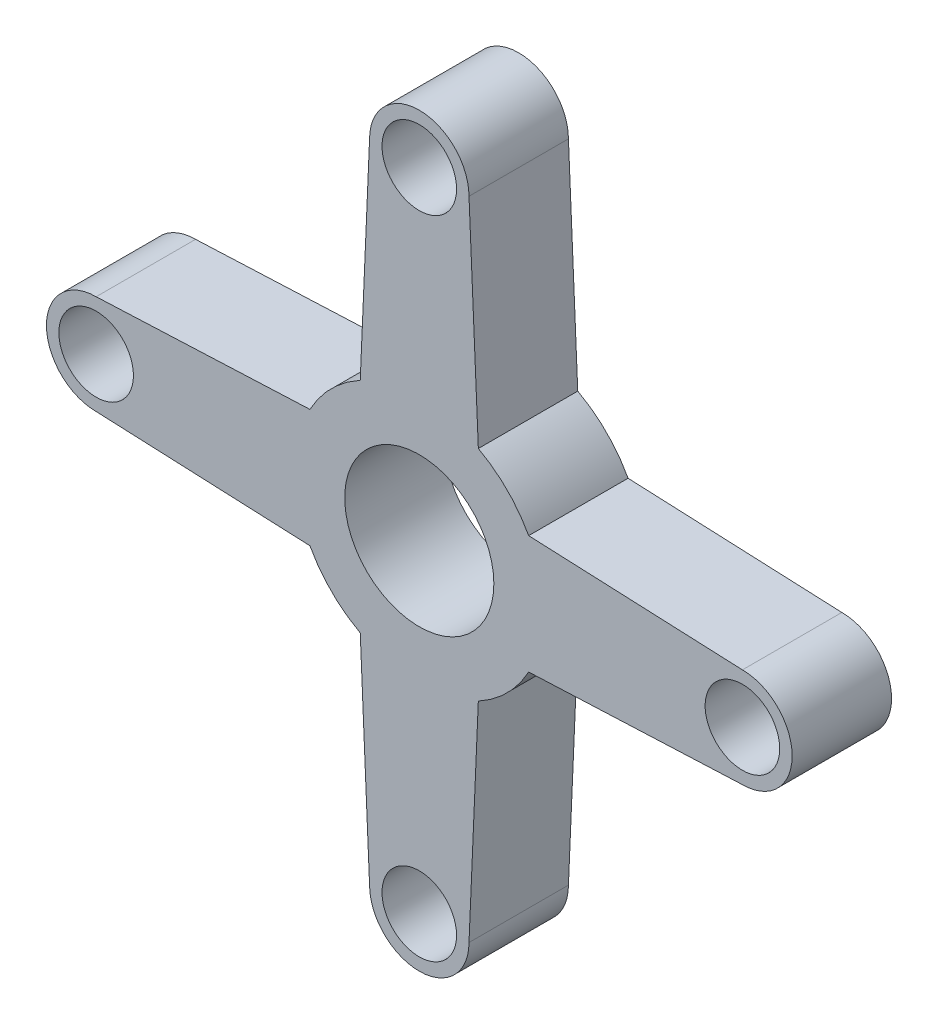
SolidWorks part; units mm, degrees
ref_plane "Front Plane" through (0, 0, 0) normal (0, 0, 1) x (1, 0, 0)
ref_plane "Top Plane" through (0, 0, 0) normal (0, 1, 0) x (1, 0, 0)
ref_plane "Right Plane" through (0, 0, 0) normal (1, 0, 0) x (0, 0, -1)
sketch "Sketch1" plane through (0, 0, 0) normal (0, 0, 1) x (1, 0, 0)
  line L0 (2, 13) -> (2.3755, 4.3997)
  line L1 (0, 0) -> (0, 13) construction
  line L2 (-2, 13) -> (-2.3755, 4.3997)
  line L3 (13, -2) -> (4.3997, -2.3755)
  line L4 (13, 2) -> (4.3997, 2.3755)
  line L5 (-2, -13) -> (-2.3755, -4.3997)
  line L6 (2, -13) -> (2.3755, -4.3997)
  line L7 (-13, 2) -> (-4.3997, 2.3755)
  line L8 (-13, -2) -> (-4.3997, -2.3755)
  circle A0 centre (0, 0) radius 3
  arc A1 (2, 13) -> (-2, 13) centre (0, 13) ccw
  arc A2 (13, -2) -> (13, 2) centre (13, 0) ccw
  arc A3 (-2, -13) -> (2, -13) centre (0, -13) ccw
  arc A4 (-13, 2) -> (-13, -2) centre (-13, 0) ccw
  arc A5 (4.3997, 2.3755) -> (2.3755, 4.3997) centre (0, 0) ccw
  arc A6 (-2.3755, 4.3997) -> (-4.3997, 2.3755) centre (0, 0) ccw
  arc A7 (-4.3997, -2.3755) -> (-2.3755, -4.3997) centre (0, 0) ccw
  arc A8 (2.3755, -4.3997) -> (4.3997, -2.3755) centre (0, 0) ccw
  circle A9 centre (0, 13) radius 1.5
  circle A10 centre (13, 0) radius 1.5
  circle A11 centre (0, -13) radius 1.5
  circle A12 centre (-13, 0) radius 1.5
  point P14 (0, 0)
  point P32 (0, 0)
  dimension "D1" = 6
  dimension "D2" = 4
  dimension "D5" = 10
  dimension "D8" = 3
  dimension "D3" = 13
  dimension "D6" = 2.5
  dimension "D4" = 4
  dimension "D7" = 4
extrude "Boss-Extrude1" add sketch "Sketch1" along normal blind 4
